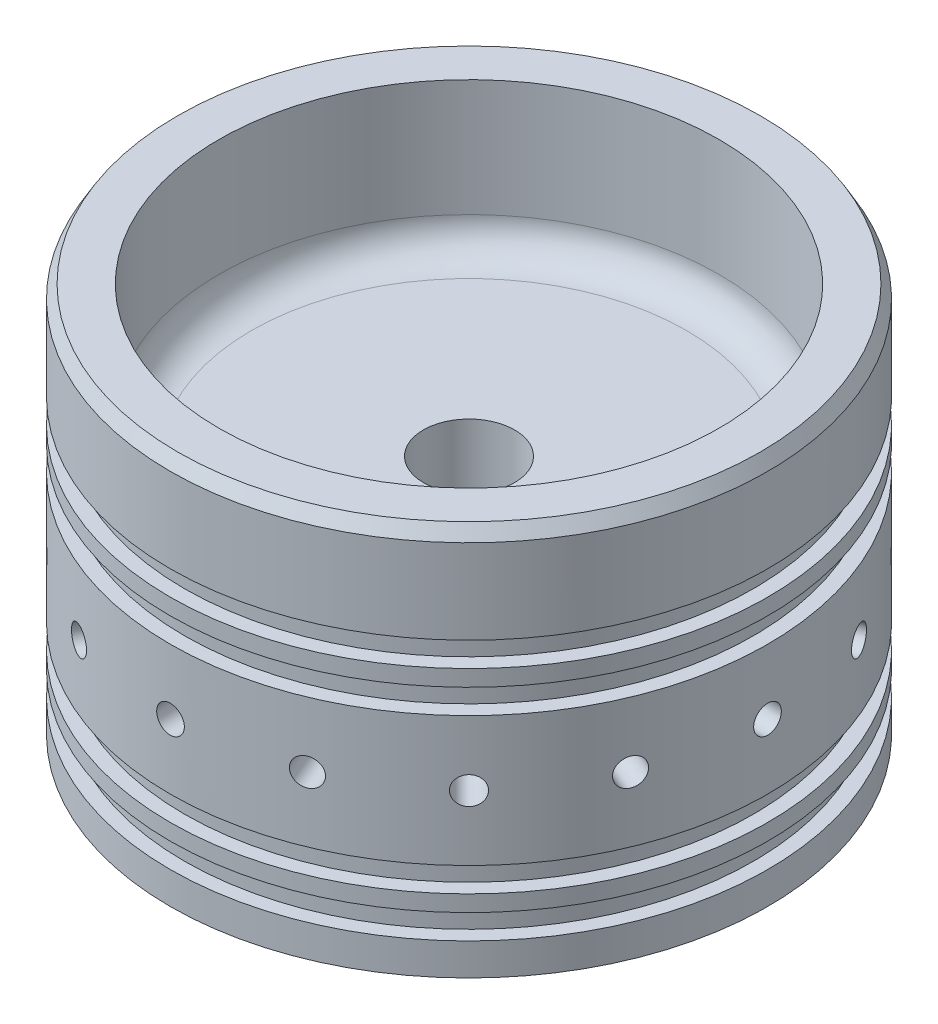
SolidWorks part; units mm, degrees
material "6061-T6 (SS)"
ref_plane "Front Plane" through (0, 0, 0) normal (0, 0, 1) x (1, 0, 0)
ref_plane "Top Plane" through (0, 0, 0) normal (0, 1, 0) x (1, 0, 0)
ref_plane "Right Plane" through (0, 0, 0) normal (1, 0, 0) x (0, 0, -1)
sketch "Sketch1" plane through (0, 0, 0) normal (0, 0, 1) x (1, 0, 0)
  line L11 (0, 0) -> (-58.4581, 0)
  line L13 (-58.4581, 44.5262) -> (-48.9331, 44.5262)
  line L14 (0, 0) -> (0, 15.3162)
  line L15 (0, 15.3162) -> (-48.9331, 15.3162)
  line L16 (-48.9331, 15.3162) -> (-48.9331, 44.5262)
  line L17 (0, 0) -> (0, -15.24)
  line L19 (-58.4581, -31.75) -> (-48.9331, -31.75)
  line L20 (-48.9331, -31.75) -> (-48.9331, -15.24)
  line L21 (-48.9331, -15.24) -> (0, -15.24)
  line L22 (0, 31.75) -> (0, -31.75) construction
  line L23 (-58.4581, 0) -> (-58.4581, 12.7)
  line L24 (-58.4581, 12.7) -> (-55.6387, 12.7)
  line L25 (-55.6387, 12.7) -> (-55.6387, 17.5006)
  line L26 (-55.6387, 17.5006) -> (-58.4581, 17.5006)
  line L27 (-58.4581, 17.5006) -> (-58.4581, 20.6756)
  line L28 (-58.4581, 20.6756) -> (-55.6387, 20.6756)
  line L29 (-55.6387, 20.6756) -> (-55.6387, 25.4762)
  line L30 (-55.6387, 25.4762) -> (-58.4581, 25.4762)
  line L31 (-58.4581, 25.4762) -> (-58.4581, 44.5262)
  line L32 (-58.4581, 0) -> (-58.4581, -12.7)
  line L33 (-58.4581, -12.7) -> (-55.6641, -12.7)
  line L34 (-55.6641, -12.7) -> (-55.6641, -17.5006)
  line L35 (-55.6641, -17.5006) -> (-58.4581, -17.5006)
  line L36 (-58.4581, -17.5006) -> (-58.4581, -20.6756)
  line L37 (-58.4581, -20.6756) -> (-55.6641, -20.6756)
  line L38 (-55.6641, -20.6756) -> (-55.6641, -25.4762)
  line L39 (-55.6641, -25.4762) -> (-58.4581, -25.4762)
  line L40 (-58.4581, -25.4762) -> (-58.4581, -31.75)
  dimension "D1" = 58.4581
  dimension "D2" = 12.7
  dimension "D3" = 4.8006
  dimension "D4" = 4.8006
  dimension "D5" = 3.175
  dimension "D6" = 2.8194
  dimension "D7" = 2.8194
  dimension "D8" = 9.525
  dimension "D9" = 12.7
  dimension "D10" = 4.8006
  dimension "D11" = 4.8006
  dimension "D12" = 3.175
  dimension "D13" = 2.794
  dimension "D14" = 2.794
  dimension "D15" = 19.05
  dimension "D16" = 9.525
revolve "Revolve1" add sketch "Sketch1" angle 360 about L22
ref_plane "HoleFacePlane" through (0, 0, 58.4581) normal (0, 0, 1) x (1, 0, 0)
sketch "HoleReference" plane through (0, 0, 58.4581) normal (0, 0, 1) x (1, 0, 0)
  point P0 (0, 0)
hole_wizard "Tap Drill for 1/4-28 Tap1" positions "Sketch3" profile "Sketch4" hole size "1/4-28" standard "ANSI Inch"
sketch "Sketch3" plane through (0, 0, 58.4581) normal (0, 0, 1) x (1, 0, 0)
  point P0 (0, 0)
sketch "Sketch4" plane through (0, 0, 58.4581) normal (1, 0, 0) x (0, -1, 0)
  line L0 (0, 0) -> (0, 20.6754)
  line L1 (0, 20.6754) -> (2.7051, 19.05)
  line L2 (2.7051, 19.05) -> (2.7051, 0)
  line L5 (2.7051, 0) -> (0, 0)
  line L10 (0, 20.6754) -> (-2.7051, 19.05) construction
  line L11 (0, -6.35) -> (0, 107.95) construction
  dimension "Hole Dia." = 5.4102
  dimension "Hole Depth" = 19.05
  dimension "Drill Angle" = 118
ref_axis "Centerline" through (0, -12.7, 0) along (0, 1, 0)
pattern_circular "HolePattern" count 16 over 360 about axis through (0, -12.7, 0) along (0, 1, 0) of "Tap Drill for 1/4-28 Tap1"
chamfer "Chamfer2" distance 2.54 angle 30 1 edges at (0, 44.5262, 58.4581)
fillet "Fillet1" radius 6.35 2 edges at (0, 15.3162, 48.9331) (0, -15.24, 48.9331)
sketch "CNVAReference" plane through (0, 15.3162, 0) normal (0, 1, 0) x (1, 0, 0)
  point P0 (0, 0)
sketch "InjectorReference" plane through (0, -15.24, 0) normal (0, -1, 0) x (1, 0, 0)
  point P0 (0, 0)
hole_wizard "Pipe Tap Drill for 1/2 Tap1" positions "Sketch7" profile "Sketch8" hole size "1/2" standard "ANSI Inch" end condition through all
sketch "Sketch7" plane through (0, 15.3162, 0) normal (0, 1, 0) x (1, 0, 0)
  point P0 (0, 0)
sketch "Sketch8" plane through (0, 15.3162, 0) normal (1, 0, 0) x (0, 0, 1)
  line L0 (0, 0) -> (0, 47.0662)
  line L1 (0, 47.0662) -> (8.9281, 47.0662)
  line L2 (8.9281, 47.0662) -> (8.9281, 0)
  line L5 (8.9281, 0) -> (0, 0)
  line L11 (0, -6.35) -> (0, 107.95) construction
  dimension "Thru Hole Dia." = 17.8562
  dimension "Thru Hole Depth" = 47.0662
